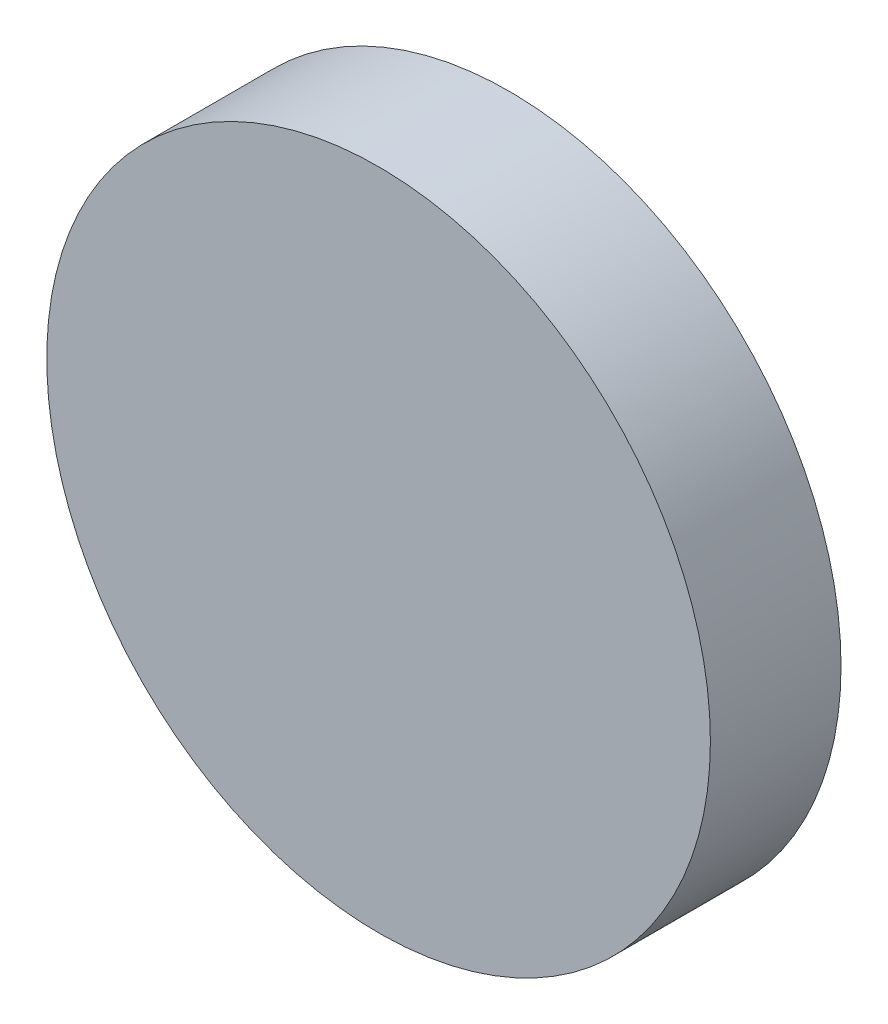
SolidWorks part; units mm, degrees
ref_plane "前视基准面" through (0, 0, 0) normal (0, 0, 1) x (1, 0, 0)
ref_plane "上视基准面" through (0, 0, 0) normal (0, 1, 0) x (1, 0, 0)
ref_plane "右视基准面" through (0, 0, 0) normal (1, 0, 0) x (0, 0, -1)
sketch "草图1" plane through (0, 0, 0) normal (0, 0, 1) x (1, 0, 0)
  circle A0 centre (0, 0) radius 25.4
  dimension "D1" = 50.8
extrude "凸台-拉伸1" add sketch "草图1" along normal blind 10
